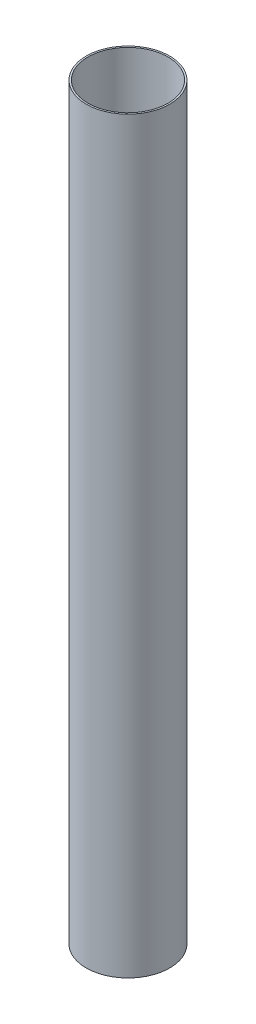
SolidWorks part; units mm, degrees
material "S-Glass Fiber"
ref_plane "Front Plane" through (0, 0, 0) normal (0, 0, 1) x (1, 0, 0)
ref_plane "Top Plane" through (0, 0, 0) normal (0, 1, 0) x (1, 0, 0)
ref_plane "Right Plane" through (0, 0, 0) normal (1, 0, 0) x (0, 0, -1)
sketch "Sketch2" plane through (0, 0, 0) normal (0, 1, 0) x (1, 0, 0)
  circle A0 centre (0, 0) radius 76.2
  circle A1 centre (0, 0) radius 79.375
  dimension "D1" = 152.4
  dimension "D2" = 158.75
extrude "Boss-Extrude1" add sketch "Sketch2" along normal blind 1422.4
